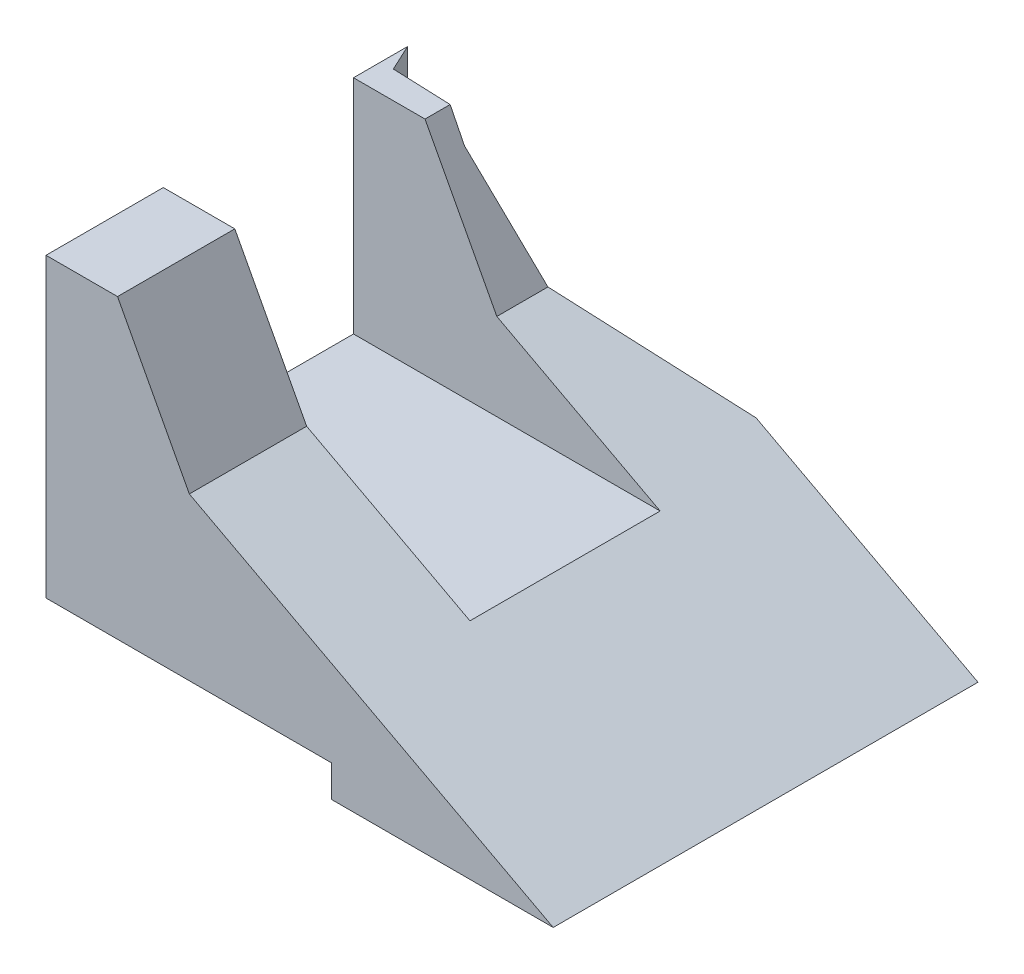
SolidWorks part; units mm, degrees
ref_plane "Alzado" through (0, 0, 0) normal (0, 0, 1) x (1, 0, 0)
ref_plane "Planta" through (0, 0, 0) normal (0, 1, 0) x (1, 0, 0)
ref_plane "Vista lateral" through (0, 0, 0) normal (1, 0, 0) x (0, 0, -1)
sketch "Croquis1" plane through (0, 0, 0) normal (1, 0, 0) x (0, 0, -1)
  line L1 (0, 0) -> (67, 0)
  line L2 (0, 0) -> (0, 51.82)
  line L3 (0, 51.82) -> (67, 51.82)
  line L4 (67, 0) -> (67, 51.82)
  dimension "D1" = 51.82
  dimension "D2" = 67
extrude "Saliente-Extruir1" add sketch "Croquis1" along normal blind 80
sketch "Croquis3" plane through (0, 0, 0) normal (0, 0, 1) x (1, 0, 0)
  line L0 (80, 0) -> (22.6084, 30.5157)
  line L1 (80, 0) -> (0, 0) construction
  line L2 (22.6084, 30.5157) -> (11.2807, 51.82)
  line L3 (80, 51.82) -> (0, 51.82) construction
  line L4 (11.2807, 51.82) -> (80, 51.82)
  line L5 (80, 51.82) -> (80, 0)
  dimension "D1" = 28
  dimension "D2" = 146
extrude "Cortar-Extruir1" cut sketch "Croquis3" against normal up to next
sketch "Croquis4" plane through (0, 51.82, 0) normal (0, 1, 0) x (1, 0, 0)
  line L0 (0, 0) -> (0, 18.5) construction
  line L1 (0, 67) -> (0, 48.5) construction
  line L2 (0, 67) -> (0, 0) construction
  line L4 (0, 18.5) -> (60, 18.5)
  line L5 (0, 18.5) -> (0, 48.5)
  line L6 (0, 48.5) -> (60, 48.5)
  line L7 (60, 18.5) -> (60, 48.5)
  dimension "D1" = 60
extrude "Cortar-Extruir2" cut sketch "Croquis4" against normal blind 35
sketch "Croquis5" plane through (0, 0, 0) normal (0, 0, 1) x (1, 0, 0)
  line L1 (0, 0) -> (45, 0)
  line L2 (0, 0) -> (0, 5)
  line L3 (0, 5) -> (45, 5)
  line L4 (45, 0) -> (45, 5)
  dimension "D1" = 5
  dimension "D2" = 45
extrude "Cortar-Extruir3" cut sketch "Croquis5" against normal up to next
sketch "Croquis6" plane through (0, 51.82, 0) normal (0, 1, 0) x (1, 0, 0)
  line L0 (4.9229, 67) -> (0, 64.3347)
  line L1 (0, 67) -> (4.9229, 67)
  line L2 (11.2807, 67) -> (0, 67) construction
  line L3 (0, 67) -> (0, 64.3347)
  line L4 (0, 67) -> (0, 48.5) construction
extrude "Cortar-Extruir4" cut sketch "Croquis6" against normal up to next
sketch "Croquis9" plane through (0, 51.82, 0) normal (0, 1, 0) x (1, 0, 0)
  line L0 (45, 67) -> (13.6262, 52.3702)
  line L1 (45, 67) -> (-4.6588, 67.0146)
  line L2 (13.6262, 52.3702) -> (1.9544, 52.8324)
  line L3 (1.9544, 52.8324) -> (-4.6588, 67.0146)
extrude "Cortar-Extruir5" cut sketch "Croquis9" against normal up to next
